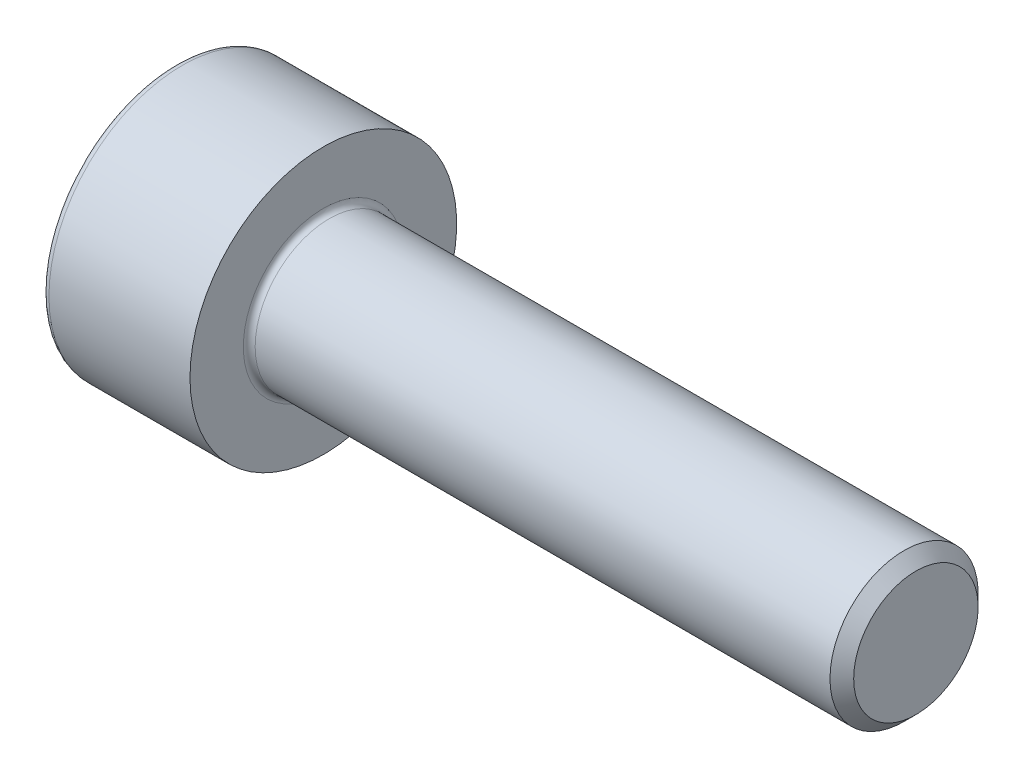
SolidWorks part; units mm, degrees
material "AISI Тип A2 Инструментальная сталь"
ref_plane "Front Plane" through (0, 0, 0) normal (0, 0, 1) x (1, 0, 0)
ref_plane "Top Plane" through (0, 0, 0) normal (0, 1, 0) x (1, 0, 0)
ref_plane "Right Plane" through (0, 0, 0) normal (1, 0, 0) x (0, 0, -1)
sketch "Sketch1" plane through (0, 0, 0) normal (0, 0, 1) x (1, 0, 0)
  line L0 (0, 0) -> (0, 2.25)
  line L1 (0, 2.25) -> (2.5, 2.25)
  line L2 (2.5, 2.25) -> (2.5, 0)
  line L3 (0, 0) -> (4.2799, 0) construction
  line L4 (2.5, 0) -> (12.5, 0)
  line L5 (12.5, 0) -> (12.5, 1.25)
  line L6 (12.5, 1.25) -> (2.5, 1.25)
  dimension "D1" = 10
  dimension "D2" = 2.5
  dimension "D3" = 2.25
  dimension "D4" = 1.25
revolve "Revolve1" add sketch "Sketch1" angle 360 about L3
fillet "Fillet1" radius 0.1 1 edges at (2.5, 0, 1.25)
fillet "Fillet2" radius 0.12 1 edges at (0, 0, 2.25)
chamfer "Chamfer1" distance 0.2 angle 45 1 edges at (12.5, 0, 1.25)
sketch "Sketch2" plane through (0, 0, 0) normal (-1, 0, 0) x (0, 0, 1)
  line L1 (0, 1.1547) -> (-1, 0.5774)
  line L2 (-1, 0.5774) -> (-1, -0.5774)
  line L3 (-1, -0.5774) -> (0, -1.1547)
  line L4 (0, -1.1547) -> (1, -0.5774)
  line L5 (1, -0.5774) -> (1, 0.5774)
  line L6 (1, 0.5774) -> (0, 1.1547)
  circle A0 centre (0, 0) radius 1 construction
  dimension "D1" = 2
extrude "Extrude1" cut sketch "Sketch2" against normal blind 1.1
